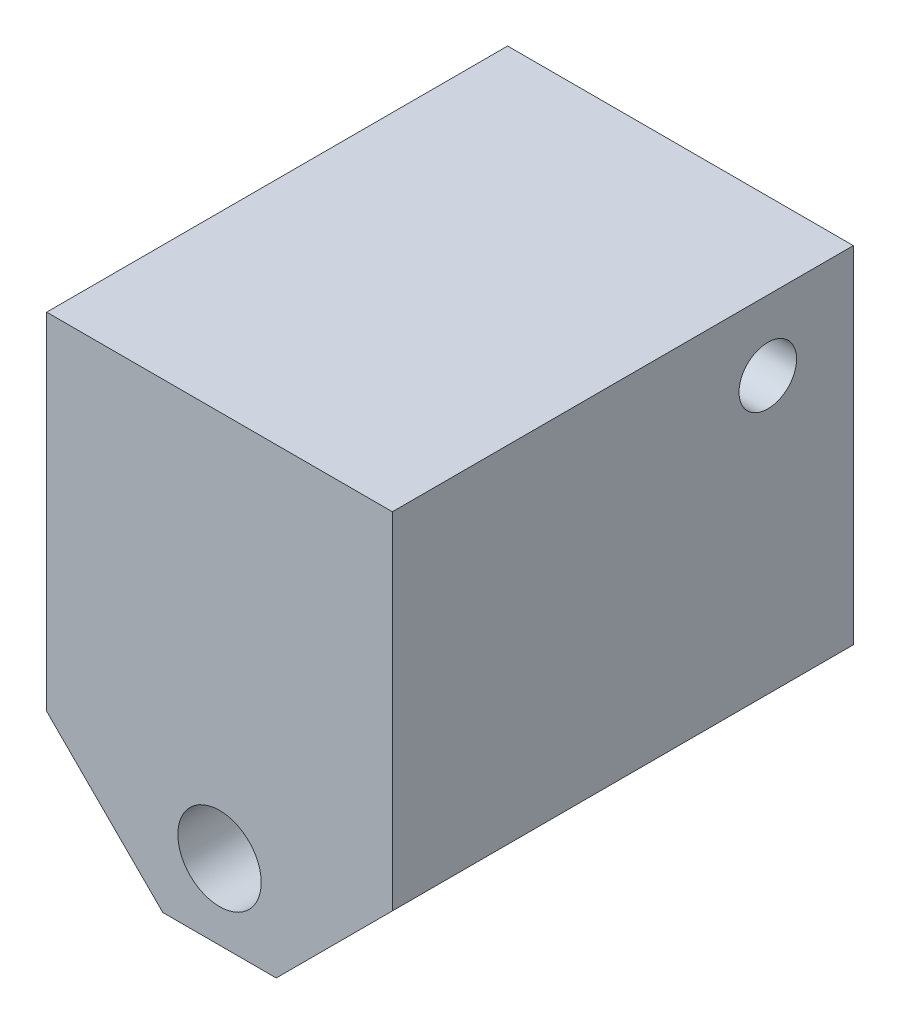
SolidWorks part; units mm, degrees
ref_plane "Front Plane" through (0, 0, 0) normal (0, 0, 1) x (1, 0, 0)
ref_plane "Top Plane" through (0, 0, 0) normal (0, 1, 0) x (1, 0, 0)
ref_plane "Right Plane" through (0, 0, 0) normal (1, 0, 0) x (0, 0, -1)
sketch "Sketch1" plane through (0, 0, 0) normal (0, 0, 1) x (1, 0, 0)
  line L0 (-15, -15) -> (-4.9223, -25.0777)
  line L1 (-15, 15) -> (15, 15)
  line L2 (-15, 15) -> (-15, -15)
  line L4 (15, 15) -> (15, -15)
  line L5 (-15, 15) -> (15, -15) construction
  line L6 (-15, -15) -> (15, 15) construction
  line L7 (-4.9223, -25.0777) -> (4.9223, -25.0777)
  line L8 (4.9223, -25.0777) -> (15, -15)
  line L9 (0, 0) -> (0, -18.5557) construction
  circle A0 centre (0, -18.5557) radius 3.6171
  point P0 (0, 0)
  dimension "D1" = 30
  dimension "D2" = 30
extrude "Boss-Extrude1" add sketch "Sketch1" along normal blind 40
hole_wizard "Ø5.0mm Dowel Hole1" positions "3DSketch1" profile "Sketch2" hole size "Ø5.0" standard "ISO" end condition through all
sketch3d "3DSketch1"
  point P0 (15, 8.9419, 7.4232)
sketch "Sketch2" plane through (15, 8.9419, 7.4232) normal (0, 1, 0) x (0, 0, -1)
  line L0 (0, 0) -> (0, 30)
  line L1 (0, 30) -> (2.5, 30)
  line L2 (2.5, 30) -> (2.5, 0)
  line L5 (2.5, 0) -> (0, 0)
  line L11 (0, -6.35) -> (0, 107.95) construction
  dimension "Thru Hole Dia." = 5
  dimension "Thru Hole Depth" = 30
